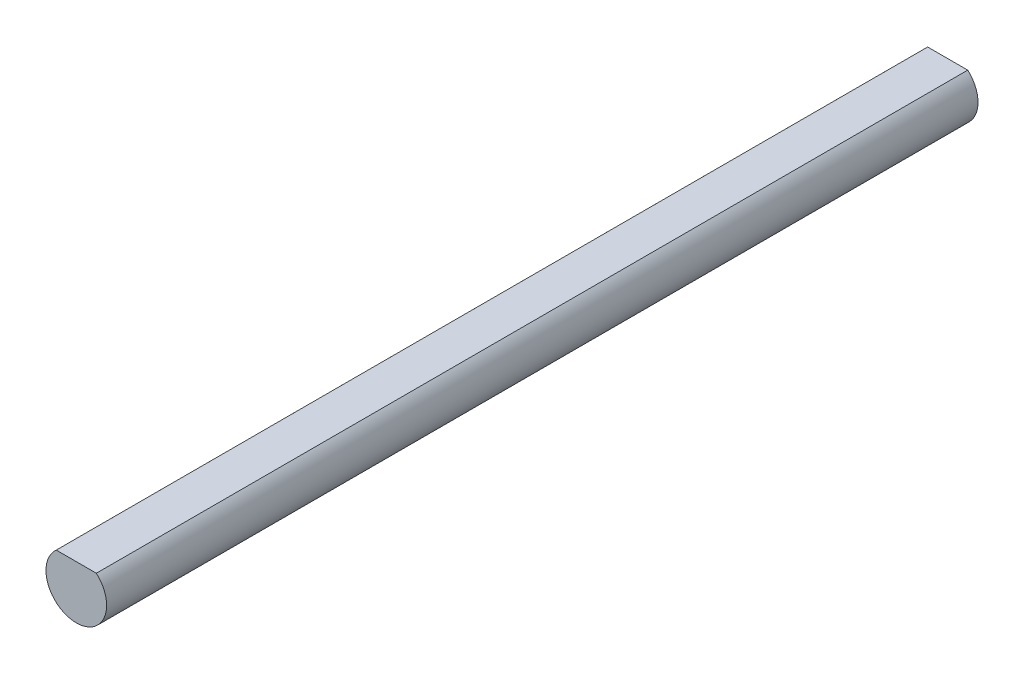
SolidWorks part; units mm, degrees
ref_plane "Front Plane" through (0, 0, 0) normal (0, 0, 1) x (1, 0, 0)
ref_plane "Top Plane" through (0, 0, 0) normal (0, 1, 0) x (1, 0, 0)
ref_plane "Right Plane" through (0, 0, 0) normal (1, 0, 0) x (0, 0, -1)
sketch "Sketch1" plane through (0, 0, 0) normal (0, 0, 1) x (1, 0, 0)
  circle A0 centre (0, 0) radius 4
  dimension "D1" = 8
extrude "Boss-Extrude1" add sketch "Sketch1" along normal blind 115
sketch "Sketch2" plane through (0, 0, 115) normal (0, 0, 1) x (1, 0, 0)
  line L0 (0, 0) -> (0, 3) construction
  line L1 (-2.6458, 3) -> (2.6458, 3)
  circle A0 centre (0, 0) radius 4 construction
  arc A1 (2.6458, 3) -> (-2.6458, 3) centre (0, 0) ccw
  dimension "D1" = 3
extrude "Cut-Extrude1" cut sketch "Sketch2" against normal up to next
